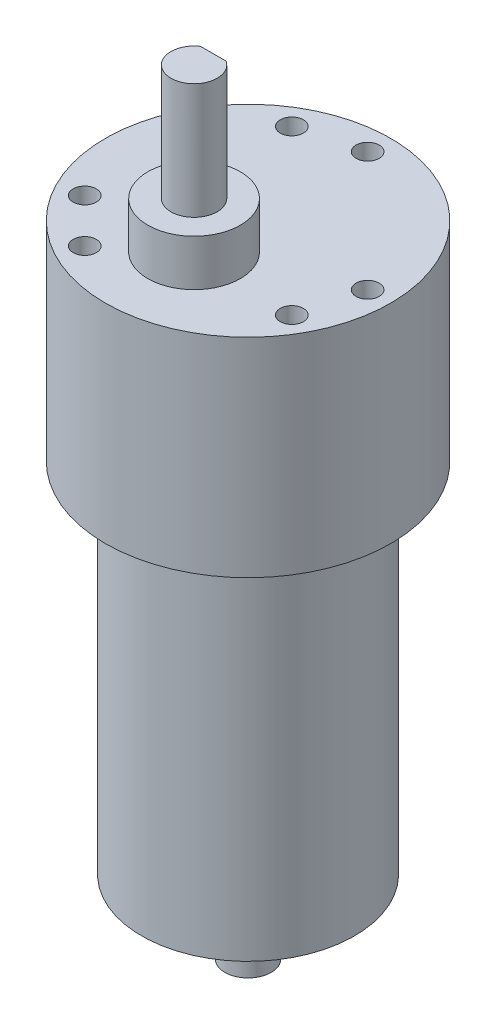
SolidWorks part; units mm, degrees
ref_plane "Front Plane" through (0, 0, 0) normal (0, 0, 1) x (1, 0, 0)
ref_plane "Top Plane" through (0, 0, 0) normal (0, 1, 0) x (1, 0, 0)
ref_plane "Right Plane" through (0, 0, 0) normal (1, 0, 0) x (0, 0, -1)
sketch "Sketch1" plane through (0, 0, 0) normal (0, 1, 0) x (1, 0, 0)
  circle A0 centre (0, 0) radius 18.5
  dimension "D1" = 37
extrude "Boss-Extrude1" add sketch "Sketch1" along normal blind 27
sketch "Sketch2" plane through (0, 27, 0) normal (0, 1, 0) x (1, 0, 0)
  circle A0 centre (0, 0) radius 15.5 construction
  circle A1 centre (0, 15.5) radius 1.5
  circle A2 centre (-7.75, 13.4234) radius 1.5
  dimension "D1" = 31
  dimension "D2" = 3
  dimension "D4" = 3
  dimension "D3" = 30
extrude "Cut-Extrude1" cut sketch "Sketch2" against normal blind 5
pattern_circular "CirPattern1" count 3 over 360 about axis through (0, 0, 0) along (0, 1, 0) of "Cut-Extrude1"
sketch "Sketch3" plane through (0, 27, 0) normal (0, 1, 0) x (1, 0, 0)
  circle A0 centre (0, -7) radius 6
  dimension "D1" = 7
  dimension "D2" = 12
extrude "Boss-Extrude2" add sketch "Sketch3" along normal blind 6
sketch "Sketch4" plane through (0, 33, 0) normal (0, 1, 0) x (1, 0, 0)
  circle A0 centre (0, -7) radius 3
  dimension "D1" = 6
extrude "Boss-Extrude3" add sketch "Sketch4" along normal blind 15
sketch "Sketch5" plane through (0, 48, 0) normal (0, 1, 0) x (1, 0, 0)
  line L0 (-1.6583, -4.5) -> (1.6583, -4.5)
  circle A0 centre (0, -7) radius 3 construction
  arc A1 (-1.6583, -4.5) -> (1.6583, -4.5) centre (0, -7) cw
  dimension "D1" = 2.5
extrude "Cut-Extrude2" cut sketch "Sketch5" against normal blind 12
sketch "Sketch6" plane through (0, 0, 0) normal (0, -1, 0) x (1, 0, 0)
  circle A0 centre (0, 0) radius 13.8
  dimension "D1" = 27.6
extrude "Boss-Extrude4" add sketch "Sketch6" along normal blind 46.4
sketch "Sketch7" plane through (0, -46.4, 0) normal (0, -1, 0) x (1, 0, 0)
  circle A0 centre (0, 0) radius 3
  dimension "D1" = 6
extrude "Boss-Extrude5" add sketch "Sketch7" along normal blind 9.5
